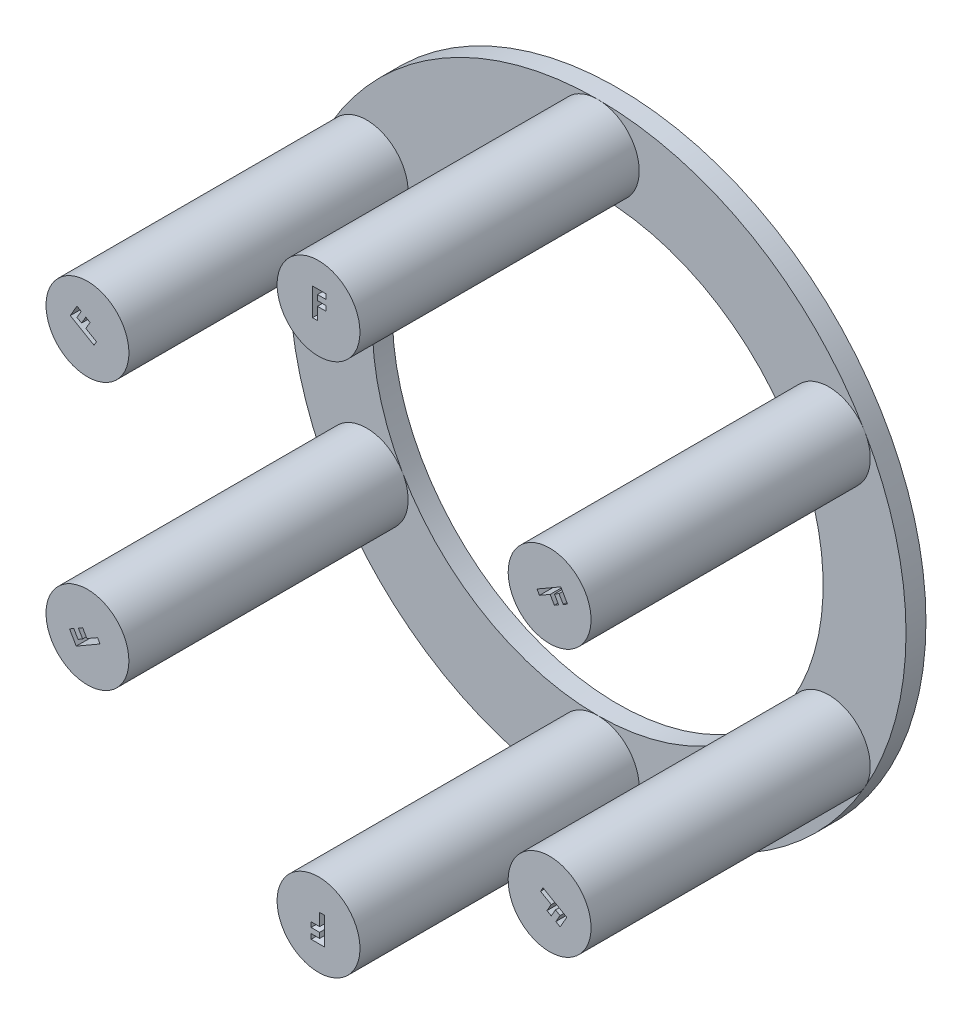
SolidWorks part; units mm, degrees
ref_plane "Front Plane" through (0, 0, 0) normal (0, 0, 1) x (1, 0, 0)
ref_plane "Top Plane" through (0, 0, 0) normal (0, 1, 0) x (1, 0, 0)
ref_plane "Right Plane" through (0, 0, 0) normal (1, 0, 0) x (0, 0, -1)
sketch "Sketch2" plane through (0, 0, 0) normal (0, 0, 1) x (1, 0, 0)
  circle A0 centre (0, 0) radius 39.2557
  circle A2 centre (0, 0) radius 28.702
  dimension "D1" = 78.5114
  dimension "D2" = 57.404
extrude "Boss-Extrude1" add sketch "Sketch2" along normal blind 2.54
sketch "Sketch3" plane through (0, 0, 2.54) normal (0, 0, 1) x (1, 0, 0)
  circle A0 centre (0, 33.9789) radius 5.2769
  circle A1 centre (0, 0) radius 39.2557 construction
  circle A2 centre (0, 0) radius 28.702 construction
  point P2 (0, 0)
extrude "Boss-Extrude2" add sketch "Sketch3" along normal blind 35.56
sketch "Sketch4" plane through (0, 0, 38.1) normal (0, 0, 1) x (1, 0, 0)
  line L0 (-5.2769, 32.5681) -> (5.2769, 32.5681) construction
  circle A2 centre (0, 33.9789) radius 5.2769 construction
  text T0 "<b>F</b>" font "Century Gothic" height 3.5
  point P6 (0, 0)
  point P9 (0, 0)
  dimension "D1" = 1.4108
extrude "Cut-Extrude1" cut sketch "Sketch4" against normal blind 2.54
pattern_circular "CirPattern1" count 6 over 360 about axis through (0, 0, 0) along (0, 0, 1) of "Boss-Extrude2", "Cut-Extrude1"
equation "\"AIRFRAME_OD\"= 3.091in"
equation "\"AIRFRAME_ID\"= 3.00in"
equation "\"FLAT_T\" = 0.125in"
equation "\"NOSE_EXP_L\"= 3.5in"
equation "\"NOSE_SHOULDER_L\" = 5in"
equation "\"MAIN_L\" = 30in"
equation "\"RECO_COUP_L\" = 6in"
equation "\"RECO_SWITCH_L\" = 1.5in"
equation "\"DROGUE_L\" = 14in"
equation "\"ATS_FORE_COUP_L\" = 4in"
equation "\"ATS_AFT_COUP_L\" = 4in"
equation "\"LOWER_L\" = 16in"
equation "\"FIN_N\" = 4"
equation "\"CR_AFT_X\" = 0.5in"
equation "\"CR_FORE_X\" = 6in"
equation "\"D1@Sketch2\"=\"AIRFRAME_OD\""
equation "\"COUPLER_OD\" = 2.998in"
equation "\"COUPLER_ID\" = 2.875in"
equation "\"RECO_ROD_X\" = 1.5in"
equation "\"ATS_ROD_X\" = 2in"
equation "\"FIN_ROOT\" = 5in"
equation "\"FIN_X\" = 0.75in"
equation "\"MOTOR_OD\" = 2.25in"
equation "\"MOTOR_ID\" = 2.126in"
equation "\"MOTOR_L\" = 8in"
equation "\"MOTOR_LOWER_X\" = 0.5in"
equation "\"D2@Sketch2\"=\"MOTOR_OD\"+0.01"
